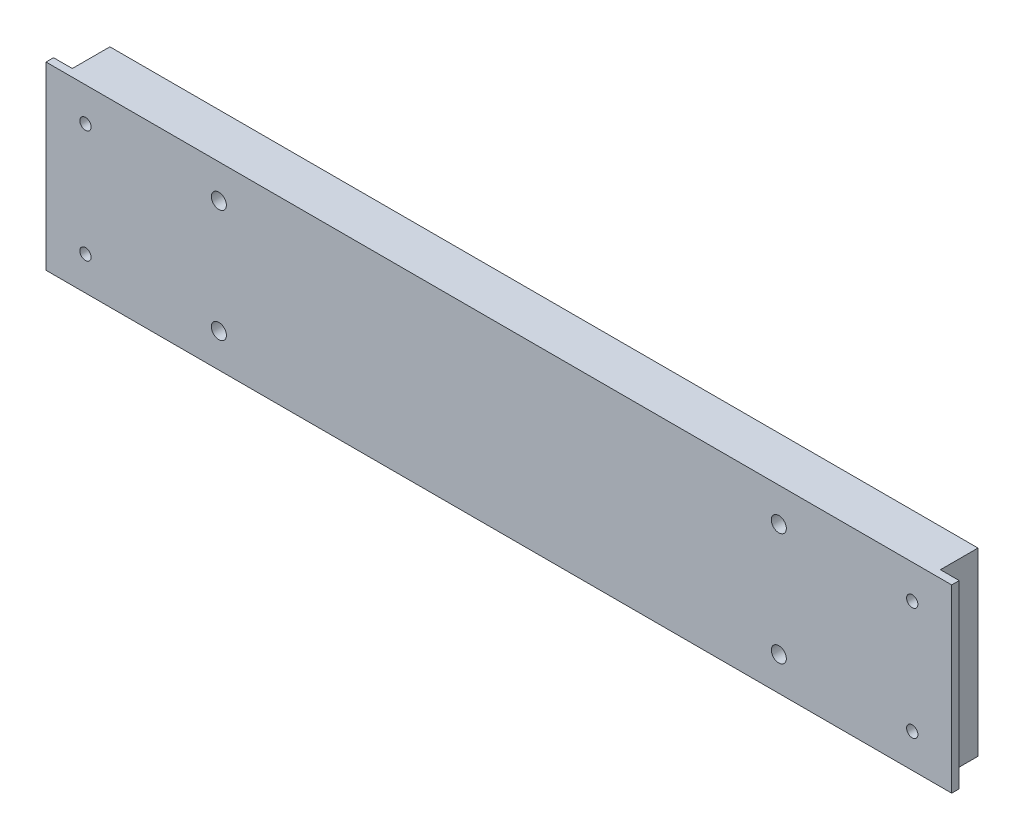
SolidWorks part; units mm, degrees
ref_plane "Plan de face" through (0, 0, 0) normal (0, 0, 1) x (1, 0, 0)
ref_plane "Plan de dessus" through (0, 0, 0) normal (0, 1, 0) x (1, 0, 0)
ref_plane "Plan de droite" through (0, 0, 0) normal (1, 0, 0) x (0, 0, -1)
sketch "Esquisse1" plane through (0, 0, 0) normal (0, 0, 1) x (1, 0, 0)
  line L0 (0, 0) -> (241, 0)
  line L1 (0, 0) -> (0, -48)
  line L2 (0, -48) -> (241, -48)
  line L3 (241, 0) -> (241, -48)
  line L4 (10.5, 0) -> (10.5, -48) construction
  line L7 (0, -24) -> (241, -24) construction
  circle A0 centre (230.5, -39) radius 1.5
  circle A1 centre (10.5, -9) radius 1.5
  circle A2 centre (10.5, -39) radius 1.5
  circle A3 centre (230.5, -9) radius 1.5
  circle A5 centre (195, -39) radius 2
  circle A6 centre (46, -9) radius 2
  circle A8 centre (46, -39) radius 2
  circle A9 centre (195, -9) radius 2
  dimension "D1" = 48
  dimension "D4" = 9
  dimension "D3" = 3
  dimension "D5" = 3
  dimension "D6" = 4
  dimension "D7" = 4
  dimension "D8" = 9
  dimension "D9" = 9
  dimension "D10" = 46
  dimension "D11" = 46
  dimension "D12" = 9
  dimension "D14" = 10.5
  dimension "D15" = 9
  dimension "D16" = 9
  dimension "D17" = 10.5
  dimension "D18" = 3
  dimension "D19" = 3
  dimension "D22" = 46
  dimension "D23" = 46
  dimension "D24" = 4
  dimension "D25" = 4
  dimension "D2" = 10.5
  dimension "D13" = 241
  dimension "D20" = 9
  dimension "D21" = 9
extrude "Extrusion1" add sketch "Esquisse1" along normal blind 12
sketch "Esquisse2" plane through (0, 0, 0) normal (0, 1, 0) x (1, 0, 0)
  line L0 (120.5, -12) -> (120.5, 0) construction
  line L1 (241, 0) -> (0, 0) construction
  line L2 (241, -12) -> (0, -12) construction
  line L3 (5, -10) -> (0, -10)
  line L4 (0, -12) -> (0, 0) construction
  line L5 (0, -10) -> (0, 0)
  line L6 (0, 0) -> (5, 0)
  line L7 (241, 0) -> (0, 0) construction
  line L8 (5, 0) -> (5, -10)
  line L9 (236, 0) -> (236, -10)
  line L10 (241, 0) -> (236, 0)
  line L11 (241, -10) -> (241, 0)
  line L12 (236, -10) -> (241, -10)
  dimension "D1" = 5
  dimension "D2" = 10
extrude "Extrusion2" cut sketch "Esquisse2" against normal through all
